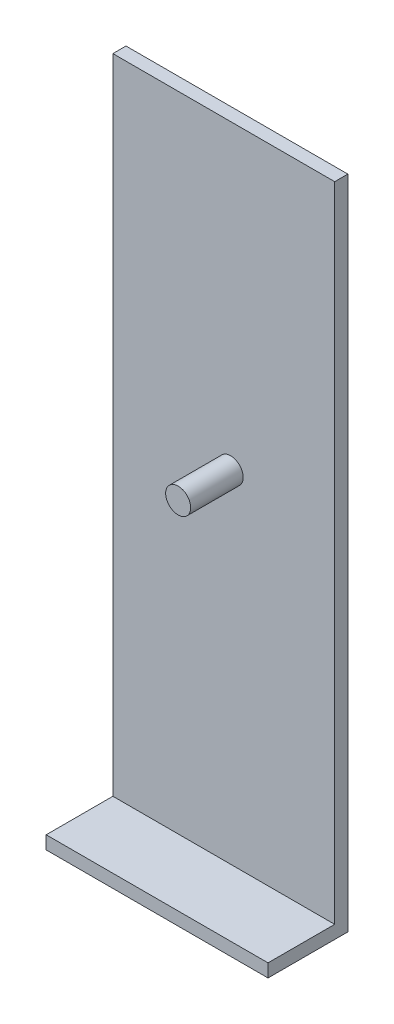
SolidWorks part; units mm, degrees
ref_plane "Front Plane" through (0, 0, 0) normal (0, 0, 1) x (1, 0, 0)
ref_plane "Top Plane" through (0, 0, 0) normal (0, 1, 0) x (1, 0, 0)
ref_plane "Right Plane" through (0, 0, 0) normal (1, 0, 0) x (0, 0, -1)
sketch "Sketch1" plane through (0, 0, 0) normal (0, 0, 1) x (1, 0, 0)
  line L1 (-42.25, -125) -> (42.25, -125)
  line L2 (-42.25, -125) -> (-42.25, 125)
  line L3 (-42.25, 125) -> (42.25, 125)
  line L4 (42.25, -125) -> (42.25, 125)
  line L5 (-42.25, -125) -> (42.25, 125) construction
  line L6 (-42.25, 125) -> (42.25, -125) construction
  point P0 (0, 0)
  dimension "D1" = 250
  dimension "D2" = 84.5
extrude "Boss-Extrude1" add sketch "Sketch1" along normal blind 5 contours L3 L4 L1 L2
sketch "Sketch2" plane through (0, 0, 5) normal (0, 0, 1) x (1, 0, 0)
  line L0 (-42.25, -125) -> (-42.25, 125) construction
  line L1 (-42.25, -120) -> (42.25, -120)
  line L2 (-42.25, -120) -> (-42.25, -125)
  line L3 (-42.25, -125) -> (42.25, -125)
  line L4 (42.25, -120) -> (42.25, -125)
  dimension "D1" = 5
extrude "Boss-Extrude2" add sketch "Sketch2" along normal blind 25.4
sketch "Sketch3" plane through (0, 0, 5) normal (0, 0, 1) x (1, 0, 0)
  line L0 (42.25, -120) -> (42.25, 125) construction
  line L1 (42.25, -120) -> (-42.25, -120) construction
  circle A0 centre (2.625, 10) radius 4.7625
  point P2 (34.4893, 28.8516)
  point P3 (15.2549, 29.1832)
  dimension "D1" = 9.525
  dimension "D2" = 39.625
  dimension "D3" = 130
extrude "Boss-Extrude3" add sketch "Sketch3" along normal blind 20
